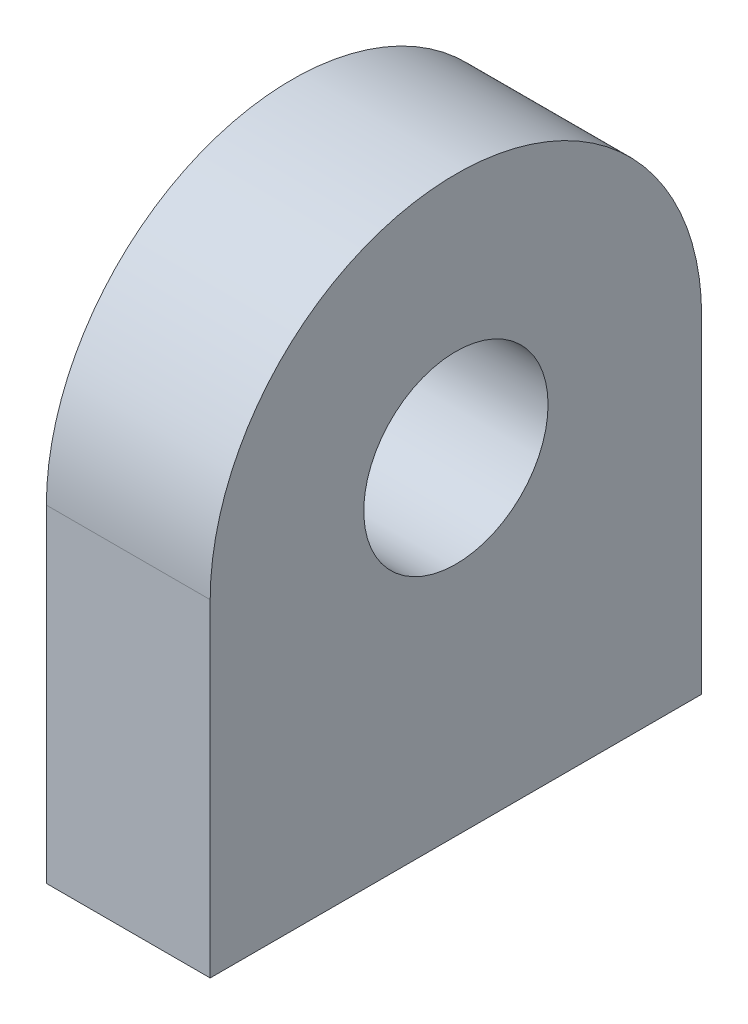
SolidWorks part; units mm, degrees
ref_plane "Front Plane" through (0, 0, 0) normal (0, 0, 1) x (1, 0, 0)
ref_plane "Top Plane" through (0, 0, 0) normal (0, 1, 0) x (1, 0, 0)
ref_plane "Right Plane" through (0, 0, 0) normal (1, 0, 0) x (0, 0, -1)
sketch "Sketch1" plane through (0, 0, 0) normal (1, 0, 0) x (0, 0, -1)
  line L0 (-38.1, 0) -> (38.1, 0)
  line L1 (38.1, 0) -> (38.1, 50.8)
  line L2 (-38.1, 0) -> (-38.1, 50.8)
  line L3 (-38.1, 50.8) -> (38.1, 50.8) construction
  arc A0 (-38.1, 50.8) -> (38.1, 50.8) centre (0, 50.8) cw
  circle A1 centre (0, 50.8) radius 14.2875
  dimension "D1" = 38.1
  dimension "D2" = 28.575
  dimension "D3" = 50.8
extrude "Boss-Extrude1" add sketch "Sketch1" along normal mid plane 25.4
sketch "Sketch2" plane through (0, 0, 0) normal (0, -1, 0) x (1, 0, 0)
  line L0 (0, 38.1) -> (0, -37.7498) construction
  line L1 (12.7, 38.1) -> (-12.7, 38.1) construction
  line L2 (-12.7, 0) -> (12.7, 0) construction
  line L3 (-12.7, 38.1) -> (-12.7, -38.1) construction
  line L4 (12.7, 38.1) -> (12.7, -38.1) construction
